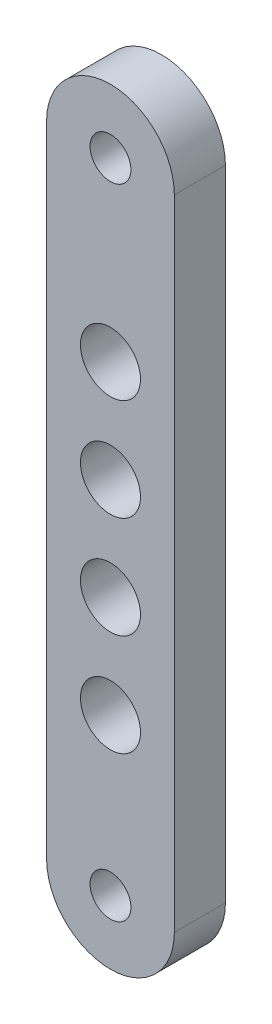
SolidWorks part; units mm, degrees
ref_plane "Front Plane" through (0, 0, 0) normal (0, 0, 1) x (1, 0, 0)
ref_plane "Top Plane" through (0, 0, 0) normal (0, 1, 0) x (1, 0, 0)
ref_plane "Right Plane" through (0, 0, 0) normal (1, 0, 0) x (0, 0, -1)
sketch "Sketch1" plane through (0, 0, 0) normal (0, 0, 1) x (1, 0, 0)
  line L0 (0, 0) -> (0, 1.6) construction
  line L1 (-5, 0) -> (5, 0) construction
  line L2 (-5, 0) -> (-5, 50)
  line L3 (-5, 50) -> (5, 50) construction
  line L4 (5, 0) -> (5, 50)
  line L5 (0, 48.4) -> (0, 50) construction
  line L6 (0, 14.58) -> (0, 33.82) construction
  line L7 (0, 36.17) -> (0, 48.4) construction
  line L8 (0, 12.23) -> (0, 0) construction
  circle A0 centre (0, 0) radius 1.6
  circle A1 centre (0, 50) radius 1.6
  arc A2 (-5, 0) -> (5, 0) centre (0, 0) ccw
  arc A3 (-5, 50) -> (5, 50) centre (0, 50) cw
  circle A4 centre (0, 36.17) radius 2.35
  circle A5 centre (0, 28.19) radius 2.35
  circle A6 centre (0, 20.21) radius 2.35
  circle A7 centre (0, 12.23) radius 2.35
  dimension "D1" = 3.2
  dimension "D4" = 4.7
  dimension "D5" = 7.98
  dimension "D2" = 10
  dimension "D3" = 50
  dimension "D6" = 7.98
  dimension "D7" = 7.98
extrude "Boss-Extrude1" add sketch "Sketch1" along normal blind 4
